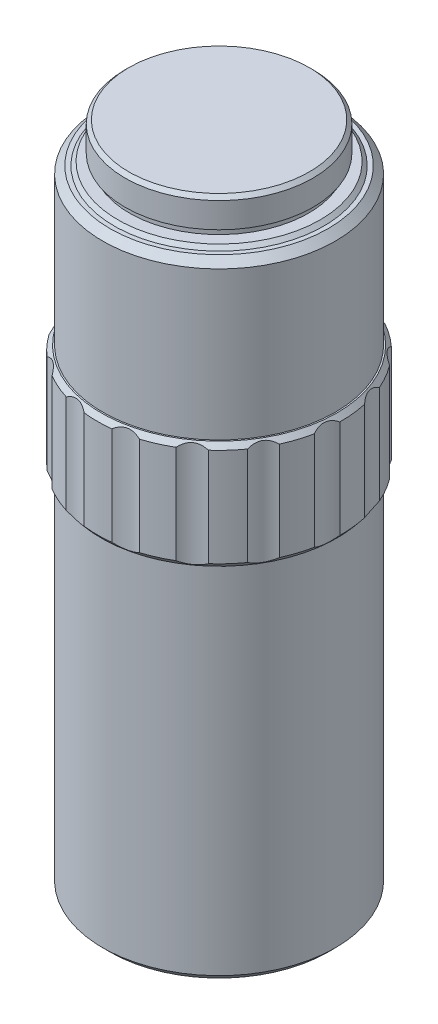
SolidWorks part; units mm, degrees
ref_plane "前视基准面" through (0, 0, 0) normal (0, 0, 1) x (1, 0, 0)
ref_plane "上视基准面" through (0, 0, 0) normal (0, 1, 0) x (1, 0, 0)
ref_plane "右视基准面" through (0, 0, 0) normal (1, 0, 0) x (0, 0, -1)
sketch "草图1" plane through (0, 0, 0) normal (0, 0, 1) x (1, 0, 0)
  line L0 (-5.725, -23.2509) -> (0, -23.2509)
  line L1 (-5.875, -23.1009) -> (-5.725, -23.2509)
  line L2 (-7, 20.7509) -> (-6.2, 20.7509)
  line L3 (-8.05, 20.0009) -> (-8.05, 9.7509)
  line L4 (-8.05, 2.2509) -> (-8.05, -22.3494)
  line L5 (-7.55, -22.8494) -> (-8.05, -22.3494)
  line L6 (-5.875, -22.8494) -> (-5.875, -23.1009)
  line L7 (-6, 23.2509) -> (-4.75, 23.2509)
  line L8 (-6.5, 23.0009) -> (-6.5, 21.2509)
  line L9 (-6.2, 21.2509) -> (-6.2, 20.7509)
  line L10 (0, 23.2509) -> (-6.25, 23.2509)
  line L11 (-6.5, 23.0009) -> (-6.25, 23.2509)
  line L12 (-6.5, 21.2509) -> (-6.2, 21.2509)
  line L13 (-8.15, 2.2509) -> (-8.05, 2.2509)
  line L14 (-8.05, 9.7509) -> (-8.15, 9.7509)
  line L15 (-5.875, -22.8494) -> (-7.55, -22.8494)
  line L16 (0, 23.2509) -> (0, -23.2509)
  line L20 (-8.4361, 2.6009) -> (-8.4361, 9.4009)
  line L21 (-8.4361, 2.6009) -> (-8.15, 2.2509)
  line L22 (-8.4361, 9.4009) -> (-8.15, 9.7509)
  line L42 (-7.25, 20.5009) -> (-7, 20.7509)
  line L43 (-7.55, 20.5009) -> (-7.25, 20.5009)
  line L44 (-8.05, 20.0009) -> (-7.55, 20.5009)
  point P23 (-2.6, 23.2509)
revolve "旋转1" add sketch "草图1" angle 360 about L16
scale "缩放比例1" scale about centroid uniform scaling yes scale factor 2
sketch "草图2" plane through (0, -45.4311, 0) normal (0, -1, 0) x (-1, 0, 0)
  circle A0 centre (0, 20.4615) radius 4
  circle A1 centre (8.3224, 18.6925) radius 4
  circle A2 centre (15.2058, 13.6914) radius 4
  circle A3 centre (19.46, 6.3229) radius 4
  circle A4 centre (20.3494, -2.1388) radius 4
  circle A5 centre (17.7201, -10.2307) radius 4
  circle A6 centre (12.0269, -16.5537) radius 4
  circle A7 centre (4.2542, -20.0143) radius 4
  circle A8 centre (-4.2542, -20.0143) radius 4
  circle A9 centre (-12.0269, -16.5537) radius 4
  circle A10 centre (-17.7201, -10.2307) radius 4
  circle A11 centre (-20.3494, -2.1388) radius 4
  circle A12 centre (-19.46, 6.3229) radius 4
  circle A13 centre (-15.2058, 13.6914) radius 4
  circle A14 centre (-8.3224, 18.6925) radius 4
  point P32 (0, 0)
  dimension "D1" = 8
  dimension "D2" = 15
extrude "切除-拉伸1" cut sketch "草图2" against normal through all
